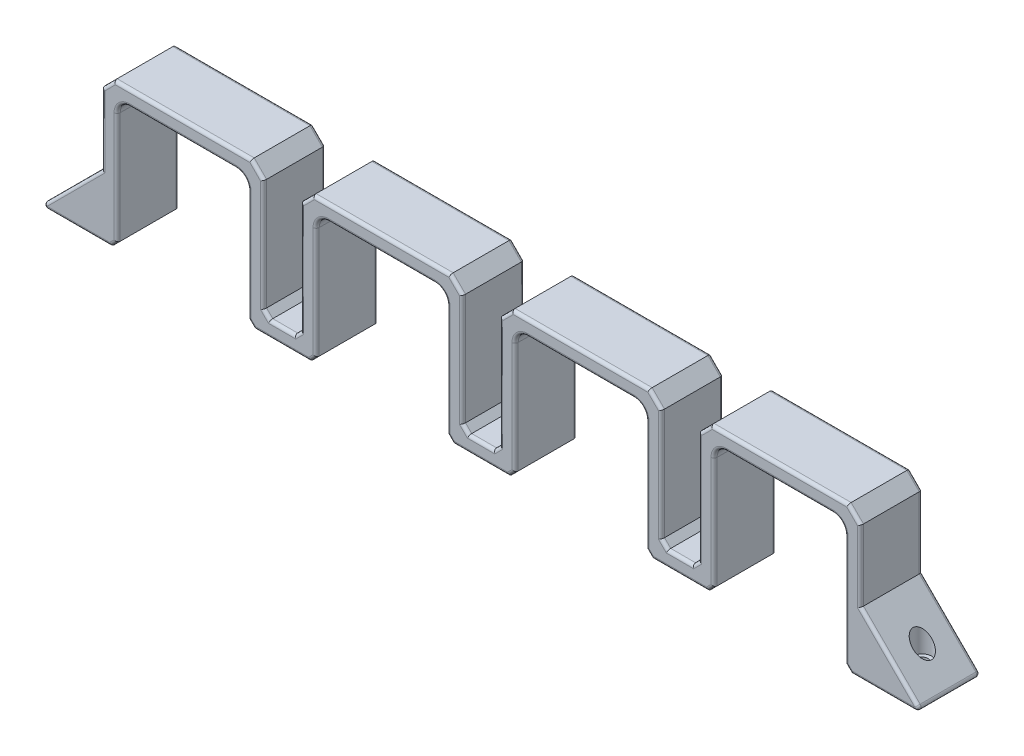
SolidWorks part; units mm, degrees
ref_plane "Front Plane" through (0, 0, 0) normal (0, 0, 1) x (1, 0, 0)
ref_plane "Top Plane" through (0, 0, 0) normal (0, 1, 0) x (1, 0, 0)
ref_plane "Right Plane" through (0, 0, 0) normal (1, 0, 0) x (0, 0, -1)
sketch "Sketch1" plane through (0, 0, 0) normal (0, 0, 1) x (1, 0, 0)
  line L0 (-26.15, 26) -> (26.15, 26)
  line L1 (-21.15, 21) -> (21.15, 21)
  line L2 (-21.15, 21) -> (-21.15, -21)
  line L4 (21.15, 21) -> (21.15, -21)
  line L5 (43.15, 21) -> (85.45, 21)
  line L6 (43.15, 21) -> (43.15, -21)
  line L8 (85.45, 21) -> (85.45, -21)
  line L9 (26.15, 26) -> (26.15, -16)
  line L10 (107.45, 21) -> (149.75, 21)
  line L11 (107.45, 21) -> (107.45, -21)
  line L13 (149.75, 21) -> (149.75, -21)
  line L15 (171.75, 21) -> (214.05, 21)
  line L16 (171.75, 21) -> (171.75, -21)
  line L18 (214.05, 21) -> (214.05, -21)
  line L19 (-26.15, 26) -> (-26.15, -21)
  line L20 (38.15, 26) -> (90.45, 26)
  line L21 (90.45, 26) -> (90.45, -16)
  line L23 (38.15, 26) -> (38.15, -16)
  line L24 (102.45, 26) -> (154.75, 26)
  line L25 (154.75, 26) -> (154.75, -16)
  line L27 (102.45, 26) -> (102.45, -16)
  line L28 (166.75, 26) -> (219.05, 26)
  line L29 (219.05, 26) -> (219.05, -21)
  line L31 (166.75, 26) -> (166.75, -16)
  line L32 (-21.15, 21) -> (21.15, -21) construction
  line L33 (26.15, -16) -> (38.15, -16)
  line L34 (90.45, -16) -> (102.45, -16)
  line L35 (154.75, -16) -> (166.75, -16)
  line L36 (-26.15, -21) -> (-21.15, -21)
  line L37 (-26.15, 26) -> (-26.15, -26) construction
  line L38 (-26.15, -26) -> (26.15, -26) construction
  line L39 (26.15, 26) -> (26.15, -26) construction
  line L40 (21.15, -21) -> (43.15, -21)
  line L41 (-21.15, -21) -> (21.15, -21) construction
  line L42 (85.45, -21) -> (107.45, -21)
  line L43 (38.15, 26) -> (38.15, -26) construction
  line L44 (38.15, -26) -> (90.45, -26) construction
  line L45 (43.15, -21) -> (85.45, -21) construction
  line L46 (154.75, 26) -> (154.75, -26) construction
  line L47 (90.45, 26) -> (90.45, -26) construction
  line L48 (102.45, 26) -> (102.45, -26) construction
  line L49 (102.45, -26) -> (154.75, -26) construction
  line L50 (166.75, 26) -> (166.75, -26) construction
  line L51 (166.75, -26) -> (219.05, -26) construction
  line L52 (219.05, 26) -> (219.05, -26) construction
  line L53 (171.75, -21) -> (214.05, -21) construction
  line L54 (214.05, -21) -> (219.05, -21)
  line L55 (107.45, -21) -> (149.75, -21) construction
  line L56 (149.75, -21) -> (171.75, -21)
  dimension "D1" = 42.3
  dimension "D2" = 42
  dimension "D3" = 4
  dimension "D4" = 22
  dimension "D5" = 5
  dimension "D6" = 5
  dimension "D7" = 5
extrude "Boss-Extrude2" add sketch "Sketch1" along normal blind 20
sketch "Sketch2" plane through (0, 0, 20) normal (0, 0, 1) x (1, 0, 0)
  line L0 (-26.15, -1) -> (-46.15, -21)
  line L1 (-26.15, 26) -> (-26.15, -21) construction
  line L2 (-46.15, -21) -> (-26.15, -21)
  line L3 (-26.15, -21) -> (-26.15, -1)
  line L4 (219.05, -21) -> (239.05, -21)
  line L5 (239.05, -21) -> (219.05, -1)
  line L6 (219.05, -21) -> (219.05, 26) construction
  line L7 (219.05, -1) -> (219.05, -21)
  dimension "D1" = 20
  dimension "D2" = 20
  dimension "D3" = 20
  dimension "D4" = 20
extrude "Boss-Extrude3" add sketch "Sketch2" against normal blind 20
sketch "Sketch3" plane through (0, 26, 0) normal (0, 1, 0) x (1, 0, 0)
  line L0 (-46.15, -10) -> (-26.15, -10) construction
  line L1 (-46.15, 0) -> (-46.15, -20) construction
  line L2 (-26.15, 0) -> (-26.15, -20) construction
  line L3 (-26.15, -10) -> (219.05, -10) construction
  line L4 (219.05, -20) -> (219.05, 0) construction
  line L5 (219.05, -10) -> (239.05, -10) construction
  line L6 (239.05, 0) -> (239.05, -20) construction
  circle A0 centre (-36.15, -10) radius 1.75
  circle A1 centre (229.05, -10) radius 1.75
  dimension "D1" = 3.5
  dimension "D2" = 3.5
extrude "Cut-Extrude1" cut sketch "Sketch3" against normal through all
sketch "Sketch4" plane through (0, 26, 0) normal (0, 1, 0) x (1, 0, 0)
  circle A0 centre (-36.15, -10) radius 3
  circle A1 centre (229.05, -10) radius 3
  dimension "D1" = 6
  dimension "D2" = 6
extrude "Cut-Extrude2" cut sketch "Sketch4" against normal offset from surface (42 mm away) 5 up to face at (-36.15, -21, 11.75)
fillet "Fillet1" radius 4 8 edges at (214.05, 21, 10) (171.75, 21, 10) (149.75, 21, 10) (107.45, 21, 10) (85.45, 21, 10) (43.15, 21, 10) (21.15, 21, 10) (-21.15, 21, 10)
chamfer "Chamfer1" distance 4 angle 45 8 edges at (219.05, 26, 10) (154.75, 26, 10) (166.75, 26, 10) (102.45, 26, 10) (90.45, 26, 10) (38.15, 26, 10) (26.15, 26, 10) (-26.15, 26, 10)
sketch "Sketch5" plane through (0, -16, 0) normal (0, 1, 0) x (1, 0, 0)
  line L0 (32.15, 0) -> (32.15, -20) construction
  line L1 (38.15, 0) -> (26.15, 0) construction
  line L2 (38.15, -20) -> (26.15, -20) construction
  line L4 (102.45, -20) -> (90.45, -20) construction
  line L5 (96.45, -20) -> (96.45, 0) construction
  line L6 (102.45, 0) -> (90.45, 0) construction
  line L8 (166.75, 0) -> (154.75, 0) construction
  line L9 (160.75, 0) -> (160.75, -20) construction
  line L10 (166.75, -20) -> (154.75, -20) construction
  circle A0 centre (32.15, -10) radius 1.75
  circle A1 centre (96.45, -10) radius 1.75
  circle A2 centre (160.75, -10) radius 1.75
  dimension "D1" = 3.5
  dimension "D2" = 3.5
  dimension "D3" = 3.5
extrude "Cut-Extrude3" cut sketch "Sketch5" against normal through all
fillet "Fillet2" radius 1 2 edges at (239.05, -21, 10) (-46.15, -21, 10)
chamfer "Chamfer2" distance 2 angle 45 14 edges at (171.75, -21, 10) (149.75, -21, 10) (107.45, -21, 10) (85.45, -21, 10) (43.15, -21, 10) (21.15, -21, 10) (214.05, -21, 10) (-21.15, -21, 10) (166.75, -16, 10) (154.75, -16, 10) (90.45, -16, 10) (102.45, -16, 10) (38.15, -16, 10) (26.15, -16, 10)
fillet "Fillet3" radius 1 132 edges at (237.5597, -20.3827, 0) (228.1964, -10.1464, 20) (228.1964, -10.1464, 0) (219.05, 10.5, 0) (217.05, 24, 0) (192.9, 26, 0) (168.75, 24, 0) (166.75, 4, 0) (165.75, -15, 0) (160.75, -16, 0) (155.75, -15, 0) (154.75, 4, 0) (152.75, 24, 0) (128.6, 26, 0) (104.45, 24, 0) (102.45, 4, 0) (101.45, -15, 0) (96.45, -16, 0) (91.45, -15, 0) (90.45, 4, 0) (88.45, 24, 0) (64.3, 26, 0) (40.15, 24, 0) (38.15, 4, 0) (37.15, -15, 0) (32.15, -16, 0) (27.15, -15, 0) (26.15, 4, 0) (24.15, 24, 0) (0, 26, 0) (-24.15, 24, 0) (-26.15, 10.5, 0) (-35.2964, -10.1464, 0) (-35.2964, -10.1464, 20) (-44.6597, -20.3827, 0) (-33.4429, -21, 0) (-22.15, -20, 0) (-21.15, -1, 0) (-19.9784, 19.8284, 0) (0, 21, 0) (19.9784, 19.8284, 0) (21.15, -1, 0) (22.15, -20, 0) (32.15, -21, 0) (42.15, -20, 0) (43.15, -1, 0) (44.3216, 19.8284, 0) (64.3, 21, 0) (84.2784, 19.8284, 0) (85.45, -1, 0) (86.45, -20, 0) (96.45, -21, 0) (106.45, -20, 0) (107.45, -1, 0) (108.6216, 19.8284, 0) (128.6, 21, 0) (148.5784, 19.8284, 0) (149.75, -1, 0) (150.75, -20, 0) (160.75, -21, 0) (170.75, -20, 0) (171.75, -1, 0) (172.9216, 19.8284, 0) (192.9, 21, 0) (212.8784, 19.8284, 0) (214.05, -1, 0) (215.05, -20, 0) (226.3429, -21, 0) (212.8784, 19.8284, 20) (192.9, 21, 20) (172.9216, 19.8284, 20) (171.75, -1, 20) (170.75, -20, 20) (160.75, -21, 20) (150.75, -20, 20) (149.75, -1, 20) (148.5784, 19.8284, 20) (128.6, 21, 20) (108.6216, 19.8284, 20) (107.45, -1, 20) (106.45, -20, 20) (96.45, -21, 20) (86.45, -20, 20) (85.45, -1, 20) (84.2784, 19.8284, 20) (64.3, 21, 20) (44.3216, 19.8284, 20) (43.15, -1, 20) (42.15, -20, 20) (32.15, -21, 20) (22.15, -20, 20) (21.15, -1, 20) (19.9784, 19.8284, 20) (0, 21, 20) (-19.9784, 19.8284, 20) (-21.15, -1, 20) (-22.15, -20, 20) (-33.4429, -21, 20) (-44.6597, -20.3827, 20) (-26.15, 10.5, 20) (-24.15, 24, 20) (0, 26, 20) (24.15, 24, 20) (26.15, 4, 20) (27.15, -15, 20) (32.15, -16, 20) (37.15, -15, 20) (38.15, 4, 20) (40.15, 24, 20) (64.3, 26, 20) (88.45, 24, 20) (90.45, 4, 20) (91.45, -15, 20) (96.45, -16, 20) (101.45, -15, 20) (102.45, 4, 20) (104.45, 24, 20) (128.6, 26, 20) (152.75, 24, 20) (154.75, 4, 20) (155.75, -15, 20) (160.75, -16, 20) (165.75, -15, 20) (166.75, 4, 20) (168.75, 24, 20) (192.9, 26, 20) (217.05, 24, 20) (219.05, 10.5, 20) (237.5597, -20.3827, 20) (226.3429, -21, 20) (215.05, -20, 20) (214.05, -1, 20)
